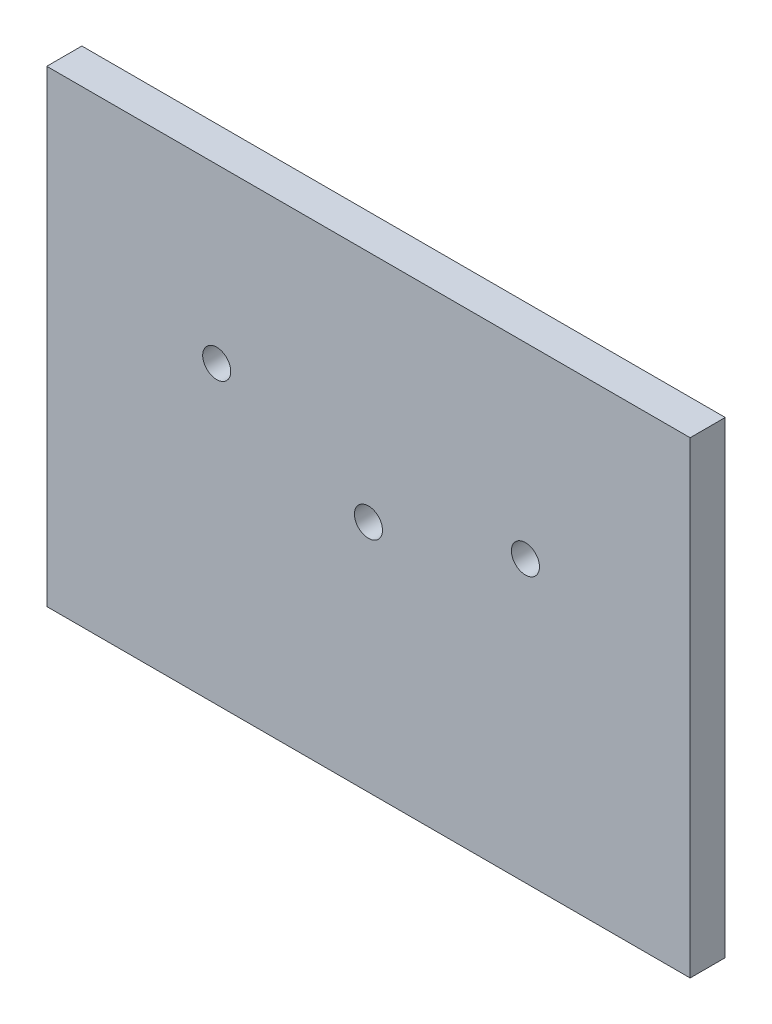
SolidWorks part; units mm, degrees
ref_plane "Plano frontal" through (0, 0, 0) normal (0, 0, 1) x (1, 0, 0)
ref_plane "Plano superior" through (0, 0, 0) normal (0, 1, 0) x (1, 0, 0)
ref_plane "Plano direito" through (0, 0, 0) normal (1, 0, 0) x (0, 0, -1)
sketch "Esboço1" plane through (0, 0, 0) normal (0, 0, 1) x (1, 0, 0)
  line L1 (-275, -200) -> (275, -200)
  line L2 (-275, -200) -> (-275, 200)
  line L3 (-275, 200) -> (275, 200)
  line L4 (275, -200) -> (275, 200)
  line L5 (-275, -200) -> (275, 200) construction
  line L6 (-275, 200) -> (275, -200) construction
  circle A1 centre (-129.7225, 52.6506) radius 12
  circle A2 centre (0, 0) radius 12
  circle A3 centre (134.1818, 39.9404) radius 12
  point P0 (0, 0)
  point P10 (0, 0)
  dimension "D3" = 24
  dimension "D4" = 24
  dimension "D7" = 24
  dimension "D1" = 400
  dimension "D2" = 550
  dimension "D5" = 140
  dimension "D6" = 145.2775
  dimension "D8" = 140
  dimension "D9" = 140.8182
extrude "Ressalto-extrusão1" add sketch "Esboço1" along normal blind 30
